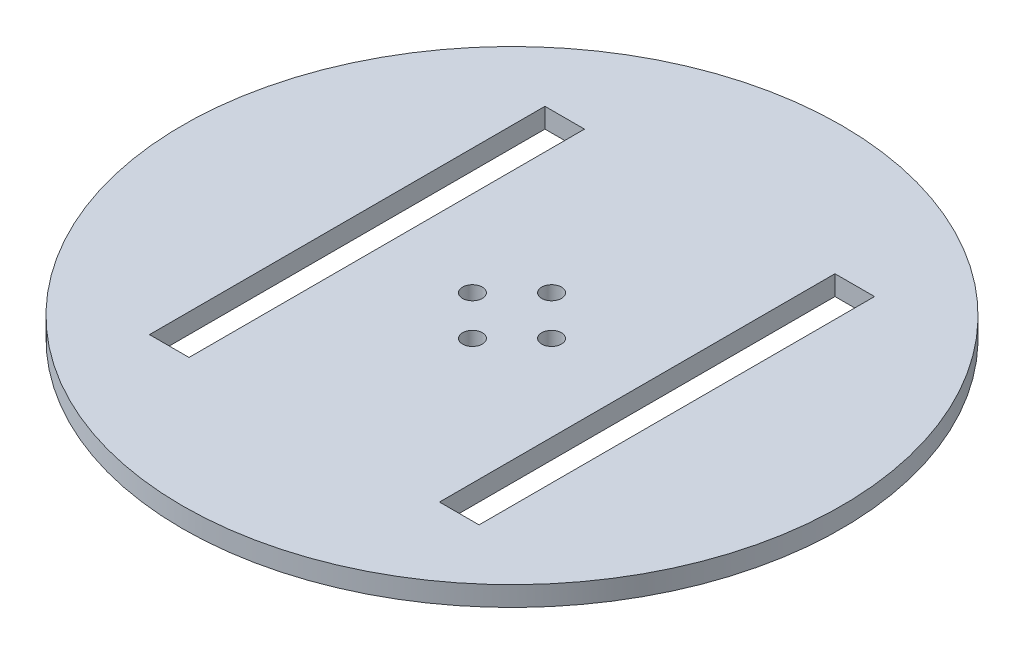
SolidWorks part; units mm, degrees
material "Balsa"
ref_plane "Alzado" through (0, 0, 0) normal (0, 0, 1) x (1, 0, 0)
ref_plane "Planta" through (0, 0, 0) normal (0, 1, 0) x (1, 0, 0)
ref_plane "Vista lateral" through (0, 0, 0) normal (1, 0, 0) x (0, 0, -1)
sketch "Croquis1" plane through (0, 0, 0) normal (0, 1, 0) x (1, 0, 0)
  circle A0 centre (0, 0) radius 50
extrude "Saliente-Extruir1" add sketch "Croquis1" along normal blind 3
sketch "Croquis2" plane through (0, 3, 0) normal (0, 1, 0) x (1, 0, 0)
  circle A0 centre (0, 6) radius 1.5
  circle A1 centre (6, 0) radius 1.5
  circle A2 centre (0, -6) radius 1.5
  circle A3 centre (-6, 0) radius 1.5
  point P0 (0, 0)
  point P1 (6, 0)
  point P3 (0, 6)
  point P4 (-6, 0)
  point P5 (0, -6)
  dimension "D5" = 3
  dimension "D1" = 6
  dimension "D2" = 6
  dimension "D3" = 6
  dimension "D4" = 6
extrude "Cortar-Extruir1" cut sketch "Croquis2" against normal up to next
sketch "Croquis3" plane through (0, 3, 0) normal (0, 1, 0) x (1, 0, 0)
  line L1 (19, 30) -> (25, 30)
  line L2 (19, 30) -> (19, -30)
  line L3 (19, -30) -> (25, -30)
  line L4 (25, 30) -> (25, -30)
  line L5 (-25, 30) -> (-19, 30)
  line L6 (-25, 30) -> (-25, -30)
  line L7 (-25, -30) -> (-19, -30)
  line L8 (-19, 30) -> (-19, -30)
  dimension "D1" = 6
  dimension "D2" = 6
  dimension "D3" = 38
  dimension "D4" = 19
  dimension "D5" = 60
  dimension "D6" = 60
  dimension "D7" = 30
  dimension "D8" = 30
extrude "Cortar-Extruir2" cut sketch "Croquis3" against normal up to next
